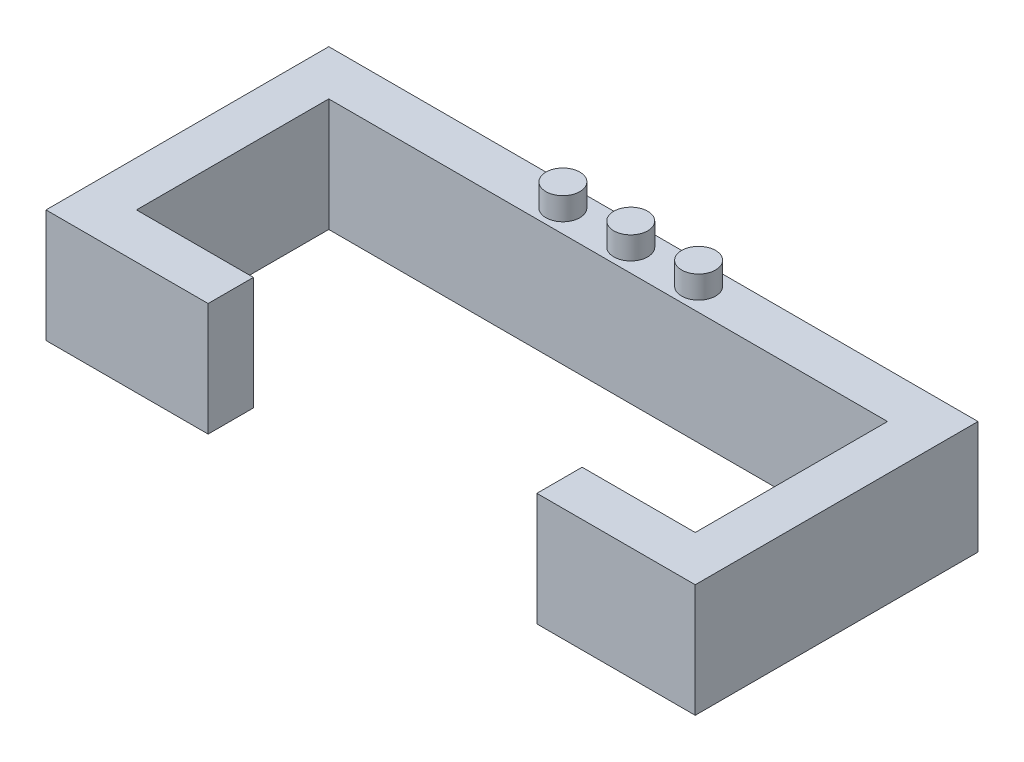
SolidWorks part; units mm, degrees
ref_plane "Front Plane" through (0, 0, 0) normal (0, 0, 1) x (1, 0, 0)
ref_plane "Top Plane" through (0, 0, 0) normal (0, 1, 0) x (1, 0, 0)
ref_plane "Right Plane" through (0, 0, 0) normal (1, 0, 0) x (0, 0, -1)
sketch "Sketch1" plane through (0, 0, 0) normal (0, 1, 0) x (1, 0, 0)
  line L0 (-12.35, 7) -> (-12.35, -1.5)
  line L1 (-12.35, -1.5) -> (12.35, -1.5)
  line L2 (-12.35, -1.5) -> (-12.35, 1.5)
  line L3 (-12.35, 1.5) -> (12.35, 1.5)
  line L4 (12.35, -1.5) -> (12.35, 1.5)
  line L5 (-12.35, -1.5) -> (12.35, 1.5) construction
  line L6 (-12.35, 1.5) -> (12.35, -1.5) construction
  line L7 (-12.35, 1.5) -> (12.35, 1.5)
  line L8 (-12.35, 1.5) -> (-12.35, 7)
  line L9 (-12.35, 7) -> (12.35, 7)
  line L10 (12.35, 1.5) -> (12.35, 7)
  line L11 (-12.35, -1.5) -> (-7.183, -1.5)
  line L12 (-7.183, -1.5) -> (-7.183, -3.5)
  line L13 (-7.183, -3.5) -> (-14.35, -3.5)
  line L14 (-14.35, -3.5) -> (-14.35, 9)
  line L15 (-14.35, 9) -> (14.35, 9)
  line L16 (14.35, 9) -> (14.35, -3.5)
  line L17 (14.35, -3.5) -> (7.35, -3.5)
  line L18 (7.35, -3.5) -> (7.35, -1.5)
  line L19 (-7.183, -1.5) -> (7.35, -1.5)
  point P0 (0, 0)
  dimension "D1" = 3
  dimension "D2" = 24.7
  dimension "D3" = 5.5
  dimension "D4" = 2
  dimension "D5" = 2
  dimension "D6" = 2
  dimension "D7" = 2
  dimension "D8" = 2
  dimension "D9" = 5
extrude "Boss-Extrude1" add sketch "Sketch1" along normal blind 5 contours L18 L17 L16 L15 L14 L13 L12 L1 L0 L9 L10 L4
sketch "Sketch2" plane through (0, 5, 0) normal (0, 1, 0) x (1, 0, 0)
  line L0 (0, -2.75) -> (0, 2.75) construction
  line L1 (-12.35, 7) -> (12.35, 7) construction
  circle A0 centre (0, 8) radius 0.75
  circle A1 centre (-3, 8) radius 0.75
  circle A3 centre (3, 8) radius 0.75
  dimension "D2" = 3
  dimension "D3" = 1
  dimension "D4" = 1
extrude "Boss-Extrude4" add sketch "Sketch2" along normal blind 1
